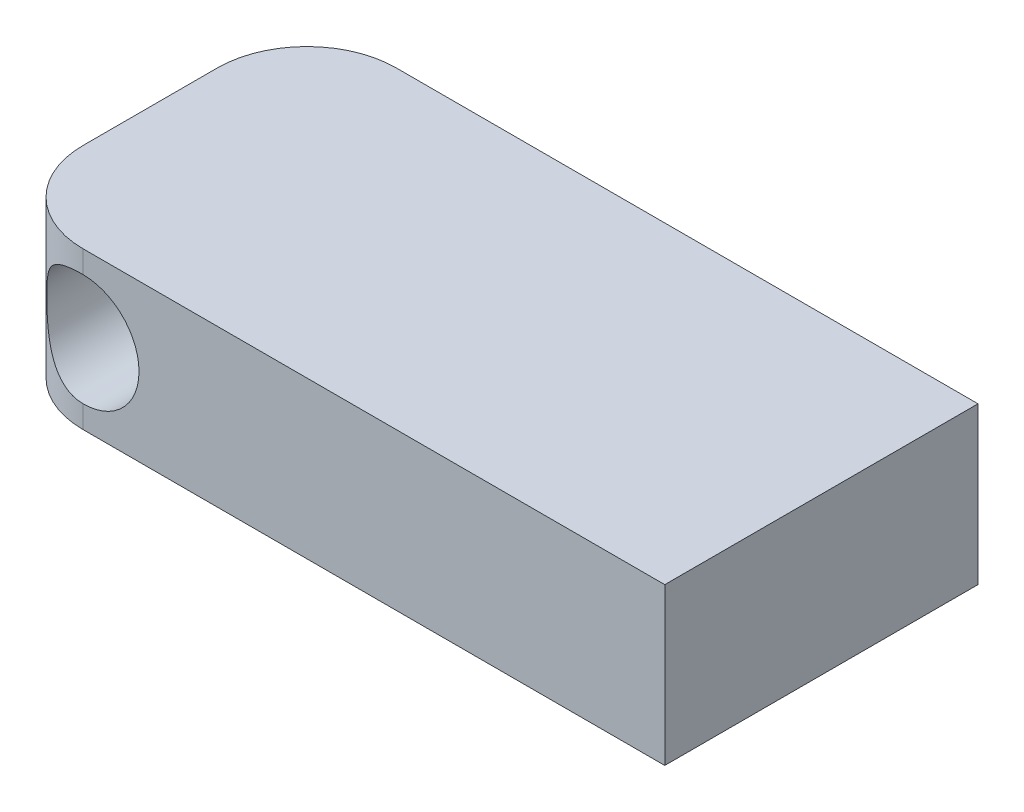
SolidWorks part; units mm, degrees
ref_plane "Front Plane" through (0, 0, 0) normal (0, 0, 1) x (1, 0, 0)
ref_plane "Top Plane" through (0, 0, 0) normal (0, 1, 0) x (1, 0, 0)
ref_plane "Right Plane" through (0, 0, 0) normal (1, 0, 0) x (0, 0, -1)
sketch "Sketch2" plane through (0, 0, 0) normal (0, 1, 0) x (1, 0, 0)
  line L1 (-2.7483, 10.6737) -> (23.2517, 10.6737)
  line L2 (-6.7483, 6.6737) -> (-6.7483, 0.6737)
  line L3 (-2.7483, -3.3263) -> (23.2517, -3.3263)
  line L4 (23.2517, 10.6737) -> (23.2517, -3.3263)
  arc A0 (-2.7483, 10.6737) -> (-6.7483, 6.6737) centre (-2.7483, 6.6737) ccw
  arc A1 (-6.7483, 0.6737) -> (-2.7483, -3.3263) centre (-2.7483, 0.6737) ccw
  point P6 (-6.7483, 10.6737)
  dimension "D3" = 4
  dimension "D1" = 30
  dimension "D2" = 14
extrude "Boss-Extrude1" add sketch "Sketch2" along normal blind 7
sketch "Sketch3" plane through (0, 0, 3.3263) normal (0, 0, 1) x (1, 0, 0)
  line L0 (-6.7483, 7) -> (-6.7483, 0) construction
  line L1 (-2.7483, 7) -> (23.2517, 7) construction
  circle A0 centre (-2.7483, 3.5) radius 2.5
  dimension "D1" = 5
  dimension "D2" = 4
  dimension "D3" = 3.5
extrude "Cut-Extrude1" cut sketch "Sketch3" against normal blind 14
